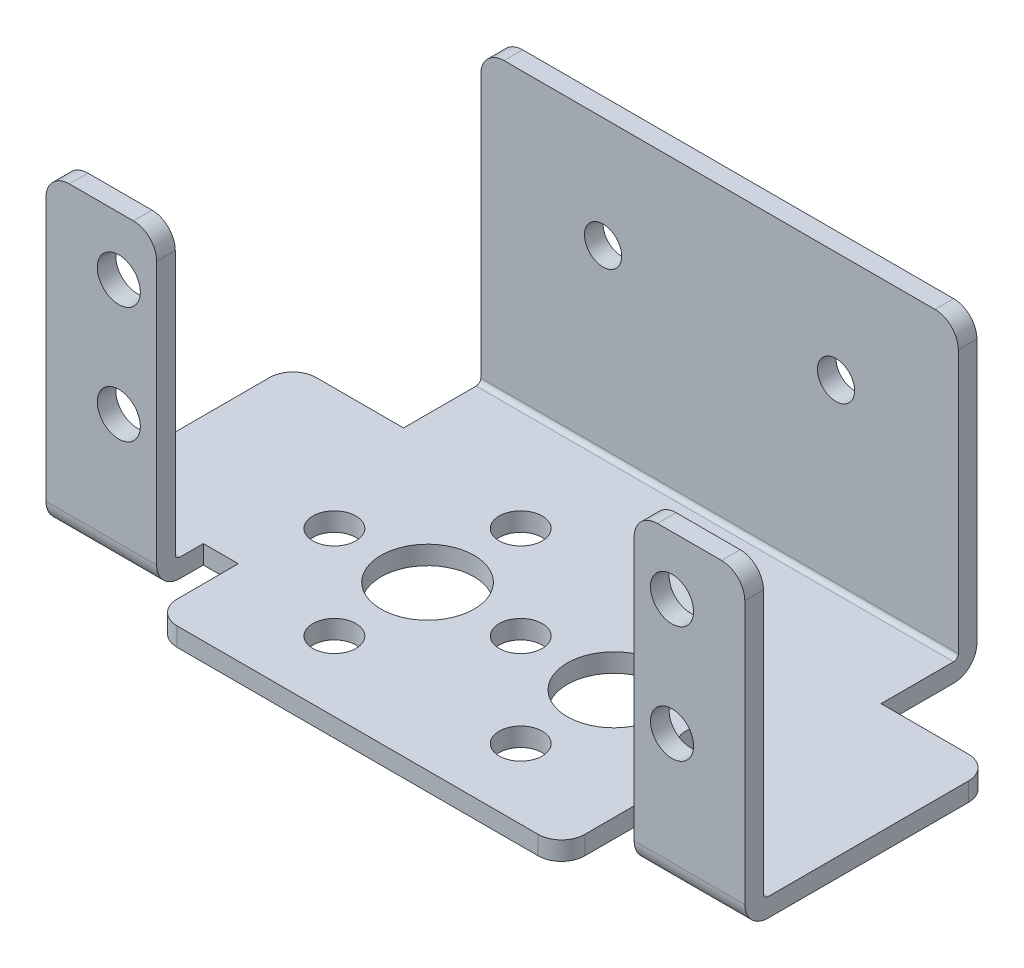
SolidWorks part; units mm, degrees
material "2024 Alloy"
ref_plane "Front Plane" through (0, 0, 0) normal (0, 0, 1) x (1, 0, 0)
ref_plane "Top Plane" through (0, 0, 0) normal (0, 1, 0) x (1, 0, 0)
ref_plane "Right Plane" through (0, 0, 0) normal (1, 0, 0) x (0, 0, -1)
ref_plane "Plane1" through (-30, 0, 0) normal (-1, 0, 0) x (0, -1, 0)
sketch "Sketch1" plane through (-30, 0, 0) normal (-1, 0, 0) x (0, -1, 0)
  line L0 (-26.6, 10.76) -> (-26.6, -18.67)
  line L1 (-26.6, -18.67) -> (0, -18.67)
  line L2 (0, -18.67) -> (0, 10.76)
  line L3 (0, 10.76) -> (-26.6, 10.76)
extrude "Boss-Extrude1" add sketch "Sketch1" against normal blind 9.5
sketch "Sketch2" plane through (-20.5, 0, 0) normal (1, 0, 0) x (0, 0, -1)
  line L0 (18.67, 26.6) -> (-9.16, 26.6)
  line L1 (-9.16, 26.6) -> (-9.16, 1.6)
  line L2 (-9.16, 1.6) -> (18.67, 1.6)
  line L3 (18.67, 1.6) -> (18.67, 26.6)
extrude "Cut-Extrude1" cut sketch "Sketch2" against normal through all
sketch "Sketch3" plane through (-20.5, 0, 0) normal (1, 0, 0) x (0, 0, -1)
  line L0 (-6.75, 1.6) -> (18.67, 1.6)
  line L1 (18.67, 1.6) -> (18.67, 0)
  line L2 (18.67, 0) -> (-6.75, 0)
  line L3 (-6.75, 0) -> (-6.75, 1.6)
extrude "Boss-Extrude2" add sketch "Sketch3" along normal blind 50.5
sketch "Sketch4" plane through (0, 0, 6.75) normal (0, 0, 1) x (1, 0, 0)
  line L0 (30, 1.6) -> (30, 0)
  line L1 (30, 0) -> (20.5, 0)
  line L2 (20.5, 0) -> (20.5, 1.6)
  line L3 (20.5, 1.6) -> (30, 1.6)
extrude "Boss-Extrude3" add sketch "Sketch4" along normal blind 4.01
sketch "Sketch5" plane through (0, 1.6, 0) normal (0, 1, 0) x (-1, 0, 0)
  line L0 (-30, 10.76) -> (-20.5, 10.76)
  line L1 (-20.5, 10.76) -> (-20.5, 9.16)
  line L2 (-20.5, 9.16) -> (-30, 9.16)
  line L3 (-30, 9.16) -> (-30, 10.76)
extrude "Boss-Extrude4" add sketch "Sketch5" along normal blind 25
sketch "Sketch6" plane through (0, 1.6, 0) normal (0, 1, 0) x (-1, 0, 0)
  line L0 (30, -10.44) -> (20.5, -10.44)
  line L1 (20.5, -10.44) -> (20.5, -18.67)
  line L2 (20.5, -18.67) -> (30, -18.67)
  line L3 (30, -18.67) -> (30, -10.44)
extrude "Cut-Extrude2" cut sketch "Sketch6" against normal through all
sketch "Sketch7" plane through (0, 1.6, 0) normal (0, 1, 0) x (-1, 0, 0)
  line L0 (-20.5, -18.67) -> (-20.5, -10.44)
  line L1 (-20.5, -10.44) -> (-30, -10.44)
  line L2 (-30, -10.44) -> (-30, -18.67)
  line L3 (-30, -18.67) -> (-20.5, -18.67)
extrude "Cut-Extrude3" cut sketch "Sketch7" against normal through all
sketch "Sketch8" plane through (0, 1.6, 0) normal (0, 1, 0) x (-1, 0, 0)
  line L0 (-20.5, -17.07) -> (20.5, -17.07)
  line L1 (20.5, -17.07) -> (20.5, -18.67)
  line L2 (20.5, -18.67) -> (-20.5, -18.67)
  line L3 (-20.5, -18.67) -> (-20.5, -17.07)
extrude "Boss-Extrude5" add sketch "Sketch8" along normal blind 25
sketch "Sketch9" plane through (0, 0, 6.75) normal (0, 0, 1) x (1, 0, 0)
  line L0 (17.5, 0) -> (-17.5, 0)
  line L1 (-17.5, 0) -> (-17.5, 1.6)
  line L2 (-17.5, 1.6) -> (17.5, 1.6)
  line L3 (17.5, 1.6) -> (17.5, 0)
extrude "Boss-Extrude6" add sketch "Sketch9" along normal blind 7.25
hole_wizard "Ø3.7 (3.7) Diameter Hole1" positions "Sketch11" profile "Sketch10" hole size "Ø3.7" standard "ANSI Metric"
sketch "Sketch11" plane through (0, 0, 0) normal (0, -1, 0) x (-1, 0, 0)
  point P0 (-16, 0)
  point P1 (-8, 8)
  point P2 (-8, -8)
  point P3 (16, 0)
  point P4 (8, 8)
  point P5 (8, -8)
  point P6 (0, 0)
sketch "Sketch10" plane through (16, 0, 0) normal (1, 0, 0) x (0, 0, -1)
  line L0 (0, 0) -> (0, 26.6)
  line L1 (0, 26.6) -> (1.85, 26.6)
  line L2 (1.85, 26.6) -> (1.85, 0)
  line L5 (1.85, 0) -> (0, 0)
  line L11 (0, -6.35) -> (0, 107.95) construction
  dimension "Thru Hole Dia." = 3.7
  dimension "Thru Hole Depth" = 26.6
hole_wizard "Ø8.0 (8) Diameter Hole1" positions "Sketch13" profile "Sketch12" hole size "Ø8.0" standard "ANSI Metric"
sketch "Sketch13" plane through (0, 0, 0) normal (0, -1, 0) x (-1, 0, 0)
  point P0 (-8, 0)
  point P1 (8, 0)
sketch "Sketch12" plane through (8, 0, 0) normal (1, 0, 0) x (0, 0, -1)
  line L0 (0, 0) -> (0, 26.6)
  line L1 (0, 26.6) -> (4, 26.6)
  line L2 (4, 26.6) -> (4, 0)
  line L5 (4, 0) -> (0, 0)
  line L11 (0, -6.35) -> (0, 107.95) construction
  dimension "Thru Hole Dia." = 8
  dimension "Thru Hole Depth" = 26.6
hole_wizard "Ø3.2 (3.2) Diameter Hole1" positions "Sketch15" profile "Sketch14" hole size "Ø3.2" standard "ANSI Metric"
sketch "Sketch15" plane through (0, 0, -18.67) normal (0, 0, -1) x (-1, 0, 0)
  point P0 (-10, 17.1)
  point P1 (10, 17.1)
sketch "Sketch14" plane through (10, 17.1, -18.67) normal (1, 0, 0) x (0, 1, 0)
  line L0 (0, 0) -> (0, 32.67)
  line L1 (0, 32.67) -> (1.6, 32.67)
  line L2 (1.6, 32.67) -> (1.6, 0)
  line L5 (1.6, 0) -> (0, 0)
  line L11 (0, -6.35) -> (0, 107.95) construction
  dimension "Thru Hole Dia." = 3.2
  dimension "Thru Hole Depth" = 32.67
hole_wizard "Ø3.7 (3.7) Diameter Hole2" positions "Sketch17" profile "Sketch16" hole size "Ø3.7" standard "ANSI Metric"
sketch "Sketch17" plane through (0, 0, 10.76) normal (0, 0, 1) x (1, 0, 0)
  point P0 (-23.75, 11.6)
  point P1 (-23.75, 21.6)
  point P2 (23.75, 11.6)
  point P3 (23.75, 21.6)
sketch "Sketch16" plane through (-23.75, 11.6, 10.76) normal (1, 0, 0) x (0, -1, 0)
  line L0 (0, 0) -> (0, 29.43)
  line L1 (0, 29.43) -> (1.85, 29.43)
  line L2 (1.85, 29.43) -> (1.85, 0)
  line L5 (1.85, 0) -> (0, 0)
  line L11 (0, -6.35) -> (0, 107.95) construction
  dimension "Thru Hole Dia." = 3.7
  dimension "Thru Hole Depth" = 29.43
fillet "Fillet1" radius 0.4 3 edges at (0, 1.6, -17.07) (-25.25, 1.6, 9.16) (25.25, 1.6, 9.16)
fillet "Fillet2" radius 2 13 edges at (-30, 0.8, -10.44) (25.25, 0, 10.76) (-17.5, 0.8, 14) (-20.5, 26.6, 9.96) (0, 0, -18.67) (20.5, 26.6, 9.96) (-25.25, 0, 10.76) (30, 26.6, 9.96) (17.5, 0.8, 14) (-20.5, 26.6, -17.87) (30, 0.8, -10.44) (20.5, 26.6, -17.87) (-30, 26.6, 9.96)
